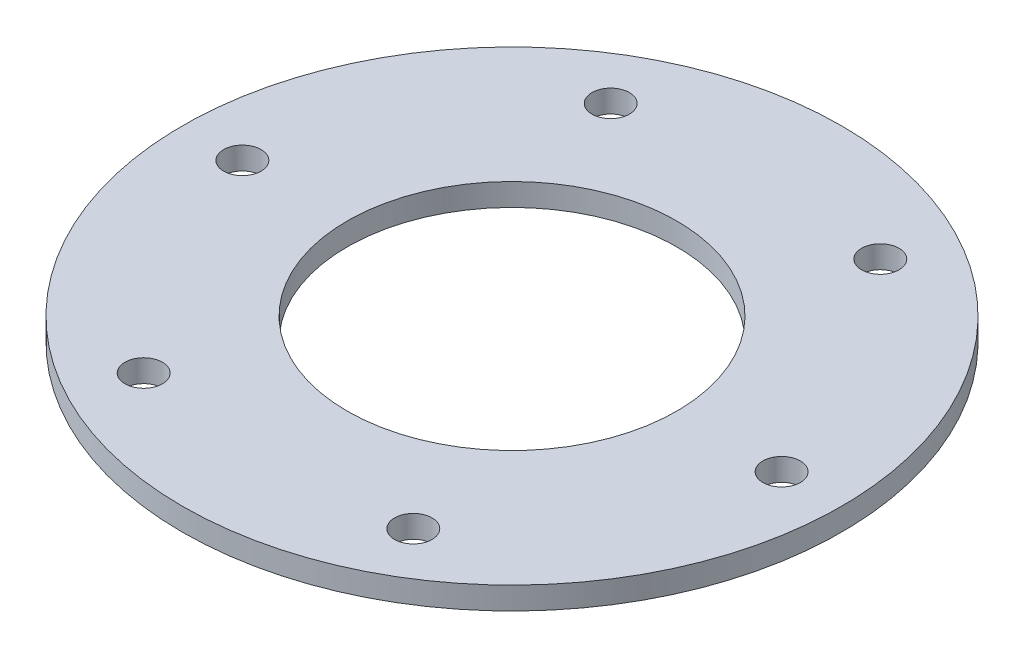
SolidWorks part; units mm, degrees
material "6061-T6 (SS)"
ref_plane "Front Plane" through (0, 0, 0) normal (0, 0, 1) x (1, 0, 0)
ref_plane "Top Plane" through (0, 0, 0) normal (0, 1, 0) x (1, 0, 0)
ref_plane "Right Plane" through (0, 0, 0) normal (1, 0, 0) x (0, 0, -1)
sketch "Sketch1" plane through (0, 0, 0) normal (0, 1, 0) x (1, 0, 0)
  circle A0 centre (-63.1889, 128.0891) radius 69.85
  circle A5 centre (-63.1889, 128.0891) radius 139.7
  point P3 (0, 0)
  dimension "D2" = 139.7
  dimension "D1" = 279.4
extrude "Boss-Extrude1" add sketch "Sketch1" along normal blind 9.525 contours A5
sketch "Sketch2" plane through (0, 9.525, 0) normal (0, 1, 0) x (1, 0, 0)
  line L0 (0, -5.2388) -> (0, 5.2388) construction
  line L3 (51.1111, 128.0891) -> (-6.0389, 227.0758) construction
  line L4 (-6.0389, 227.0758) -> (-120.3389, 227.0758) construction
  line L5 (-120.3389, 227.0758) -> (-177.4889, 128.0891) construction
  line L6 (-177.4889, 128.0891) -> (-120.3389, 29.1024) construction
  line L7 (-120.3389, 29.1024) -> (-6.0389, 29.1024) construction
  line L8 (-6.0389, 29.1024) -> (51.1111, 128.0891) construction
  circle A1 centre (-63.1889, 128.0891) radius 98.9867 construction
  circle A2 centre (51.1111, 128.0891) radius 7.9375
  circle A3 centre (-6.0389, 227.0758) radius 7.9375
  circle A4 centre (-120.3389, 227.0758) radius 7.9375
  circle A5 centre (-177.4889, 128.0891) radius 7.9375
  circle A6 centre (-120.3389, 29.1024) radius 7.9375
  circle A7 centre (-6.0389, 29.1024) radius 7.9375
  dimension "D2" = 15.875
  dimension "D3" = 15.875
  dimension "D4" = 15.875
  dimension "D5" = 15.875
  dimension "D6" = 15.875
  dimension "D7" = 15.875
  dimension "D1" = 228.6
extrude "Cut-Extrude1" cut sketch "Sketch2" against normal up to next
equation "\"thread_rod_size\"= 5 / 8"
equation "\"D2@Sketch2\"=\"thread_rod_size\""
equation "\"D3@Sketch2\"=\"thread_rod_size\""
equation "\"D4@Sketch2\"=\"thread_rod_size\""
equation "\"D5@Sketch2\"=\"thread_rod_size\""
equation "\"D6@Sketch2\"=\"thread_rod_size\""
equation "\"D7@Sketch2\"=\"thread_rod_size\""
